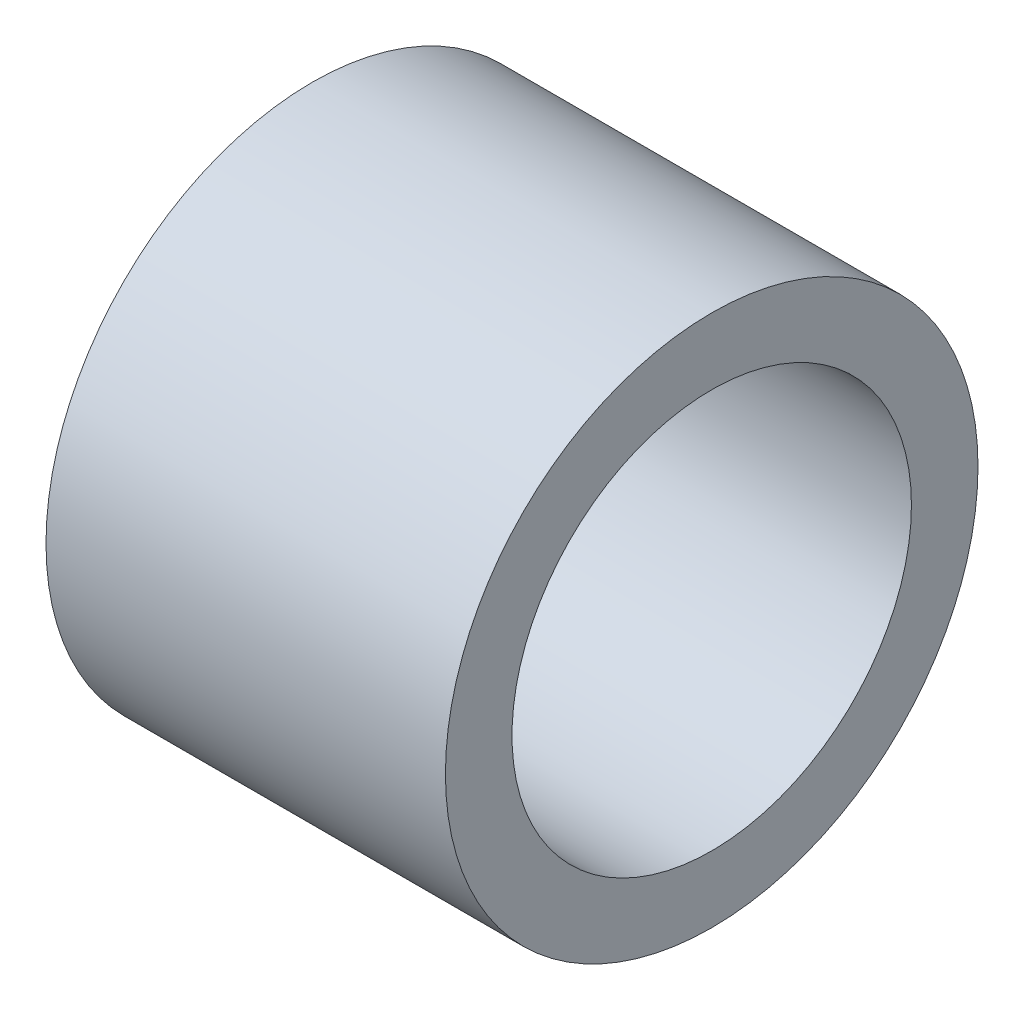
SolidWorks part; units mm, degrees
ref_plane "Alzado" through (0, 0, 0) normal (0, 0, 1) x (1, 0, 0)
ref_plane "Planta" through (0, 0, 0) normal (0, 1, 0) x (1, 0, 0)
ref_plane "Vista lateral" through (0, 0, 0) normal (1, 0, 0) x (0, 0, -1)
sketch "Croquis1" plane through (0, 0, 0) normal (1, 0, 0) x (0, 0, -1)
  circle A0 centre (0, 0) radius 9.525
  circle A1 centre (0, 0) radius 12.7
  dimension "D1" = 19.05
  dimension "D2" = 25.4
extrude "Saliente-Extruir1" add sketch "Croquis1" along normal mid plane 19.05
